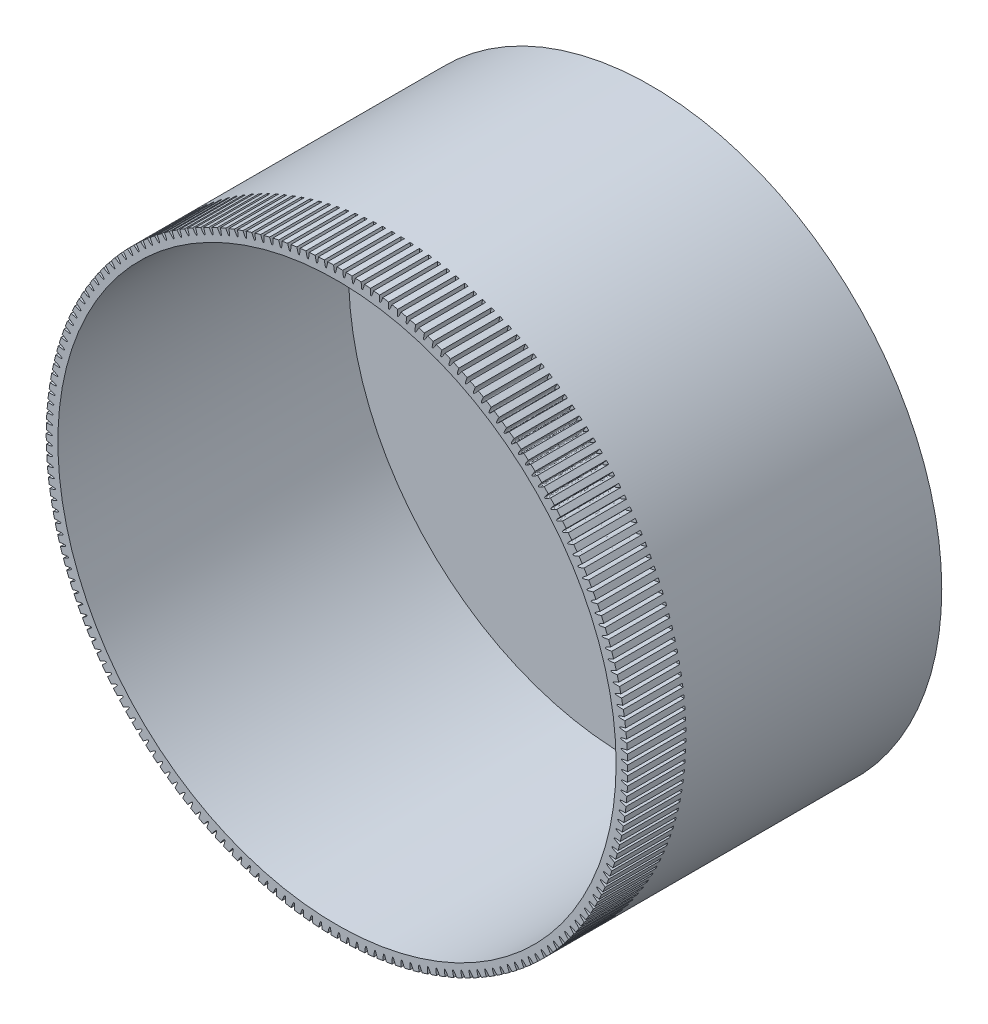
SolidWorks part; units mm, degrees
ref_plane "前视基准面" through (0, 0, 0) normal (0, 0, 1) x (1, 0, 0)
ref_plane "上视基准面" through (0, 0, 0) normal (0, 1, 0) x (1, 0, 0)
ref_plane "右视基准面" through (0, 0, 0) normal (1, 0, 0) x (0, 0, -1)
sketch "草图1" plane through (0, 0, 0) normal (0, 0, 1) x (1, 0, 0)
  circle A0 centre (0, 0) radius 25
  point P4 (-219.3856, 19.7922)
extrude "凸台-拉伸1" add sketch "草图1" along normal blind 27
sketch "草图2" plane through (0, 0, 27) normal (0, 0, 1) x (1, 0, 0)
  circle A0 centre (0, 0) radius 24
extrude "切除-拉伸1" cut sketch "草图2" against normal blind 25
sketch "草图3" plane through (0, 0, 2) normal (0, 0, 1) x (1, 0, 0)
  circle A0 centre (0, 0) radius 5
extrude "切除-拉伸2" cut sketch "草图3" against normal blind 25
sketch "草图4" plane through (0, 0, 27) normal (0, 0, 1) x (1, 0, 0)
  line L0 (-25.0876, 3.651) -> (-25.1488, 3.2839)
  spline S0 degree 2 poles (-25.0876, 3.651) (-23.3847, 3.1622) (-25.1488, 3.2839) knots 0 0 0 1 1 1
extrude "切除-拉伸5" cut sketch "草图4" against normal blind 5
pattern_circular "阵列(圆周)1" count 198 over 360 about axis through (0, 0, 27) along (0, 0, -1) of "切除-拉伸5"
